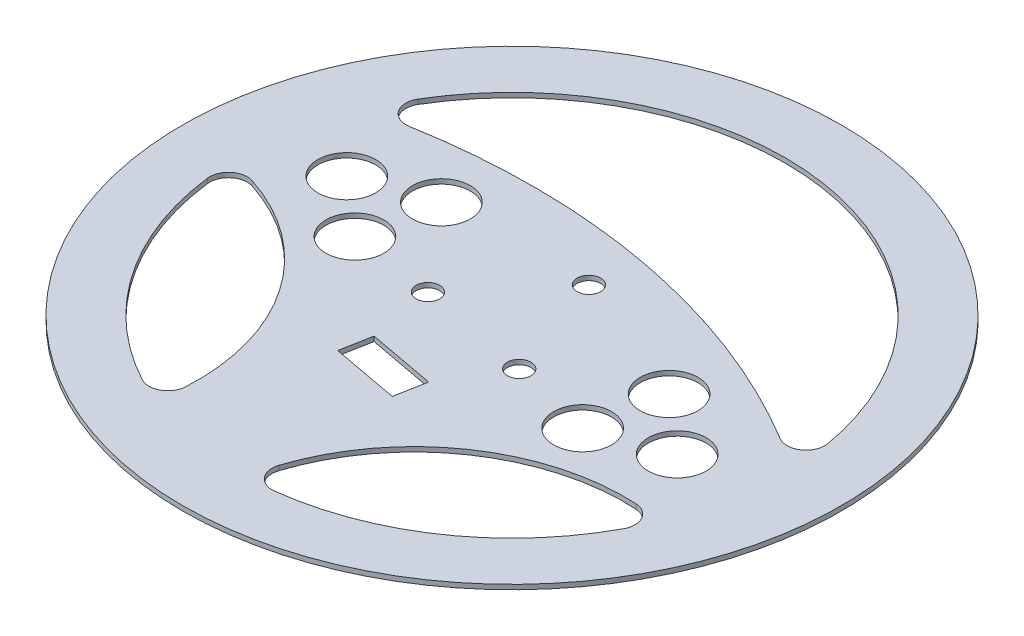
SolidWorks part; units mm, degrees
material "Thornel Mat VMA"
ref_plane "Front Plane" through (0, 0, 0) normal (0, 0, 1) x (1, 0, 0)
ref_plane "Top Plane" through (0, 0, 0) normal (0, 1, 0) x (1, 0, 0)
ref_plane "Right Plane" through (0, 0, 0) normal (1, 0, 0) x (0, 0, -1)
sketch "Sketch1" plane through (0, 0, 0) normal (0, 1, 0) x (1, 0, 0)
  line L0 (-121.9716, 24.7971) -> (121.9716, -20.6629) construction
  line L1 (-49.4776, -1.4277) -> (-44.8976, 23.1492) construction
  line L4 (-49.4776, -1.4277) -> (-68.4718, 14.8272) construction
  line L6 (3.52, -41.8169) -> (5.4436, -31.4946)
  line L7 (-19.0907, -37.6033) -> (3.52, -41.8169)
  line L8 (-17.1671, -27.281) -> (-19.0907, -37.6033)
  line L9 (5.4436, -31.4946) -> (-17.1671, -27.281)
  line L10 (-4.0716, -19.7817) -> (4.0716, 23.916) construction
  line L11 (92.0481, 4.2915) -> (85.0682, -33.1637) construction
  line L14 (-92.0481, -0.1572) -> (-85.0682, 37.2979) construction
  line L15 (22.1926, 121.1548) -> (-22.1926, -117.0206) construction
  line L18 (-35.2308, -83.0011) -> (2.2244, -89.981) construction
  circle A11 centre (0, 2.0671) radius 111.125
  circle A17 centre (4.0716, 23.916) radius 3.9688
  circle A18 centre (-20.9575, -5.3312) radius 3.9688
  circle A19 centre (16.8858, -12.3835) radius 3.9688
  circle A32 centre (-44.8976, 23.1492) radius 9.75
  circle A33 centre (-49.4776, -1.4277) radius 9.75
  circle A34 centre (-68.4718, 14.8272) radius 9.75
  circle A35 centre (68.4718, -10.6929) radius 9.75
  circle A36 centre (44.8976, -19.015) radius 9.75
  circle A37 centre (49.4776, 5.5619) radius 9.75
  arc A38 (90.7192, 17.8096) -> (-78.9593, 49.43) centre (0, 2.0671) ccw
  arc A39 (-34.1335, -73.8465) -> (-83.1128, -2.4311) centre (-105.0614, -69.9878) ccw
  arc A40 (4.4982, -81.0457) -> (75.9136, -32.0664) centre (72.0549, -102.9943) cw
  arc A41 (81.1819, 11.2871) -> (-72.4115, 39.91) centre (-33.7849, -179.2264) ccw
  arc A42 (11.318, -89.3096) -> (81.1663, -41.4051) centre (0, 2.0671) ccw
  arc A43 (-91.3767, -9.2509) -> (-43.4722, -79.0992) centre (0, 2.0671) ccw
  arc A44 (81.1819, 11.2871) -> (90.7192, 17.8096) centre (84.4627, 16.7239) ccw
  arc A45 (75.9136, -32.0664) -> (81.1663, -41.4051) centre (75.5686, -38.407) cw
  arc A46 (4.4982, -81.0457) -> (11.318, -89.3096) centre (10.5375, -83.0078) ccw
  arc A47 (-34.1335, -73.8465) -> (-43.4722, -79.0992) centre (-40.4741, -73.5015) cw
  arc A48 (-83.1128, -2.4311) -> (-91.3767, -9.2509) centre (-85.0749, -8.4703) ccw
  arc A49 (-72.4115, 39.91) -> (-78.9593, 49.43) centre (-73.5138, 46.1636) cw
  point P7 (0, 2.0671)
  point P12 (0.4915, 2.2309)
  point P21 (0, 2.0671)
  point P23 (-47.1876, 10.8607)
  point P31 (88.5582, -14.4361)
  point P34 (-88.5582, 18.5703)
  point P36 (0, 2.0671)
  point P40 (-16.5032, -86.491)
  point P43 (6.9799, 39.5223)
  dimension "D1" = 184.15
  dimension "D2" = 25
  dimension "D4" = 48
  dimension "D5" = 19.5
  dimension "D11" = 38.1
  dimension "D12" = 38.1
  dimension "D13" = 6.35
  dimension "D6" = 19.5
  dimension "D7" = 19.5
  dimension "D8" = 19.05
  dimension "D9" = 38.1
  dimension "D3" = 25
  dimension "D10" = 38.1
extrude "Boss-Extrude1" add sketch "Sketch1" along normal blind 1.5875
